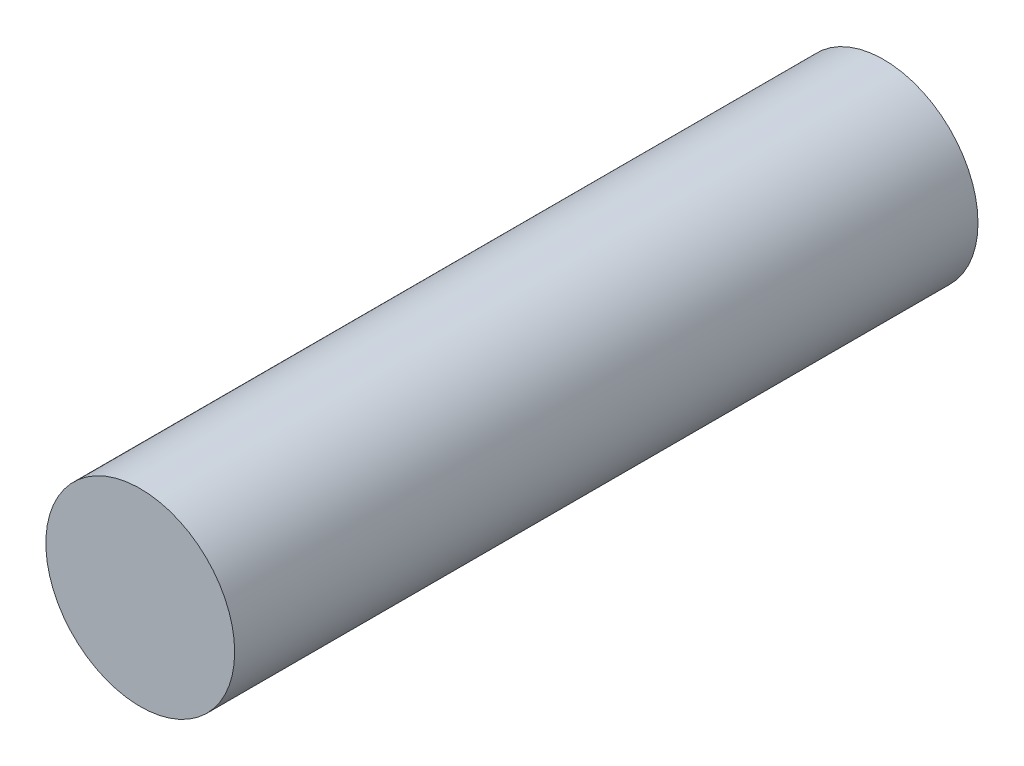
SolidWorks part; units mm, degrees
ref_plane "Front Plane" through (0, 0, 0) normal (0, 0, 1) x (1, 0, 0)
ref_plane "Top Plane" through (0, 0, 0) normal (0, 1, 0) x (1, 0, 0)
ref_plane "Right Plane" through (0, 0, 0) normal (1, 0, 0) x (0, 0, -1)
sketch "Sketch1" plane through (0, 0, 0) normal (0, 0, 1) x (1, 0, 0)
  circle A0 centre (0, 0) radius 6.35
  dimension "D1" = 12.7
extrude "Boss-Extrude1" add sketch "Sketch1" along normal blind 50
